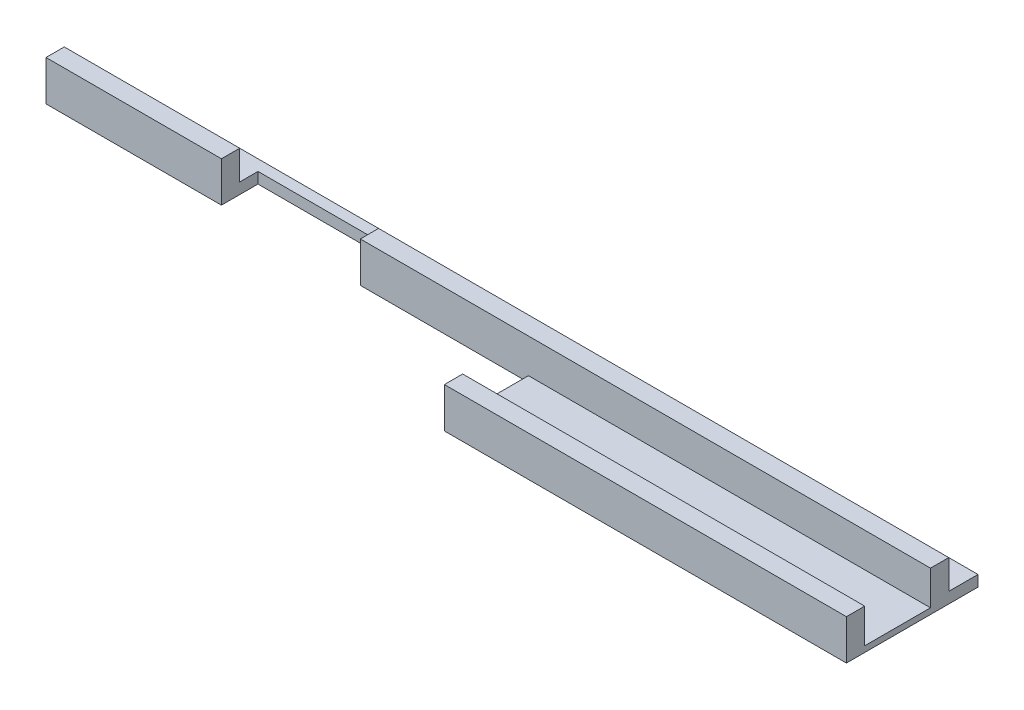
SolidWorks part; units mm, degrees
ref_plane "Front Plane" through (0, 0, 0) normal (0, 0, 1) x (1, 0, 0)
ref_plane "Top Plane" through (0, 0, 0) normal (0, 1, 0) x (1, 0, 0)
ref_plane "Right Plane" through (0, 0, 0) normal (1, 0, 0) x (0, 0, -1)
sketch "Sketch1" plane through (0, 0, 0) normal (0, 1, 0) x (1, 0, 0)
  line L1 (-60, -68.5) -> (60, -68.5)
  line L2 (-60, -68.5) -> (-60, 68.5)
  line L3 (-60, 68.5) -> (60, 68.5)
  line L4 (60, -68.5) -> (60, 68.5)
  line L5 (-60, -68.5) -> (60, 68.5) construction
  line L6 (-60, 68.5) -> (60, -68.5) construction
  point P0 (0, 0)
  dimension "D1" = 137
  dimension "D2" = 120
extrude "Boss-Extrude1" add sketch "Sketch1" along normal blind 3
sketch "Sketch2" plane through (0, 3, 0) normal (0, 1, 0) x (1, 0, 0)
  line L0 (60, -68.5) -> (60, 68.5) construction
  line L1 (-60, -68.5) -> (60, -68.5)
  line L2 (-60, -68.5) -> (-60, -63.5)
  line L3 (-60, -63.5) -> (60, -63.5)
  line L4 (60, -68.5) -> (60, -63.5)
  dimension "D1" = 5
extrude "Boss-Extrude2" add sketch "Sketch2" along normal blind 8
sketch "Sketch3" plane through (0, 11, 0) normal (0, 1, 0) x (1, 0, 0)
  line L1 (-19, -58.5) -> (19, -58.5)
  line L2 (-19, -58.5) -> (-19, -68.5)
  line L3 (-19, -68.5) -> (19, -68.5)
  line L4 (19, -58.5) -> (19, -68.5)
  line L5 (-60, -68.5) -> (60, -68.5) construction
  line L6 (0, 0) -> (0, -68.5) construction
  dimension "D1" = 38
  dimension "D3" = 10
extrude "Cut-Extrude1" cut sketch "Sketch3" against normal blind 25
sketch "Sketch4" plane through (0, 3, 0) normal (0, 1, 0) x (1, 0, 0)
  line L1 (-60, 68.5) -> (60, 68.5)
  line L2 (-60, 68.5) -> (-60, -55.5)
  line L3 (-60, -55.5) -> (60, -55.5)
  line L4 (60, 68.5) -> (60, -55.5)
  line L5 (-60, -68.5) -> (-19, -68.5) construction
  line L6 (60, -63.5) -> (60, 68.5) construction
  dimension "D1" = 13
extrude "Cut-Extrude2" cut sketch "Sketch4" against normal through all both and the other way through all
sketch "Sketch7" plane through (-60, 0, 0) normal (-1, 0, 0) x (0, 0, 1)
  line L0 (63.5, 11) -> (63.5, 3)
  line L1 (63.5, 3) -> (55.5, 3)
  line L2 (63.5, 11) -> (68.5, 11)
  line L3 (68.5, 11) -> (68.5, 0)
  line L4 (68.5, 0) -> (55.5, 0)
  line L5 (55.5, 0) -> (55.5, 3)
extrude "Boss-Extrude3" add sketch "Sketch7" along normal blind 7
sketch "Sketch8" plane through (60, 0, 0) normal (1, 0, 0) x (0, 0, -1)
  line L0 (-55.5, 0) -> (-55.5, 3)
  line L1 (-55.5, 3) -> (-63.5, 3)
  line L2 (-63.5, 3) -> (-63.5, 11)
  line L3 (-63.5, 11) -> (-68.5, 11)
  line L4 (-68.5, 11) -> (-68.5, 1.6)
  line L5 (-68.5, 11) -> (-68.5, 0) construction
  line L6 (-68.5, 1.6) -> (-86.5, 1.6)
  line L7 (-86.5, 1.6) -> (-86.5, 11)
  line L8 (-86.5, 11) -> (-91.5, 11)
  line L9 (-91.5, 11) -> (-91.5, 0)
  line L10 (-91.5, 0) -> (-55.5, 0)
  dimension "D1" = 5
  dimension "D2" = 18
  dimension "D3" = 1.4
extrude "Boss-Extrude4" add sketch "Sketch8" along normal blind 120
sketch "Sketch9" plane through (0, 11, 0) normal (0, 1, 0) x (1, 0, 0)
  line L0 (180, -91.5) -> (60, -91.5) construction
  line L1 (60, -68.5) -> (65, -68.5)
  line L2 (60, -68.5) -> (60, -91.5)
  line L3 (60, -91.5) -> (65, -91.5)
  line L4 (65, -68.5) -> (65, -91.5)
  dimension "D1" = 5
extrude "Cut-Extrude3" cut sketch "Sketch9" against normal blind 250
other "Move Face1" face at (180, 5.32, 73.1) parameters "D1"=5
